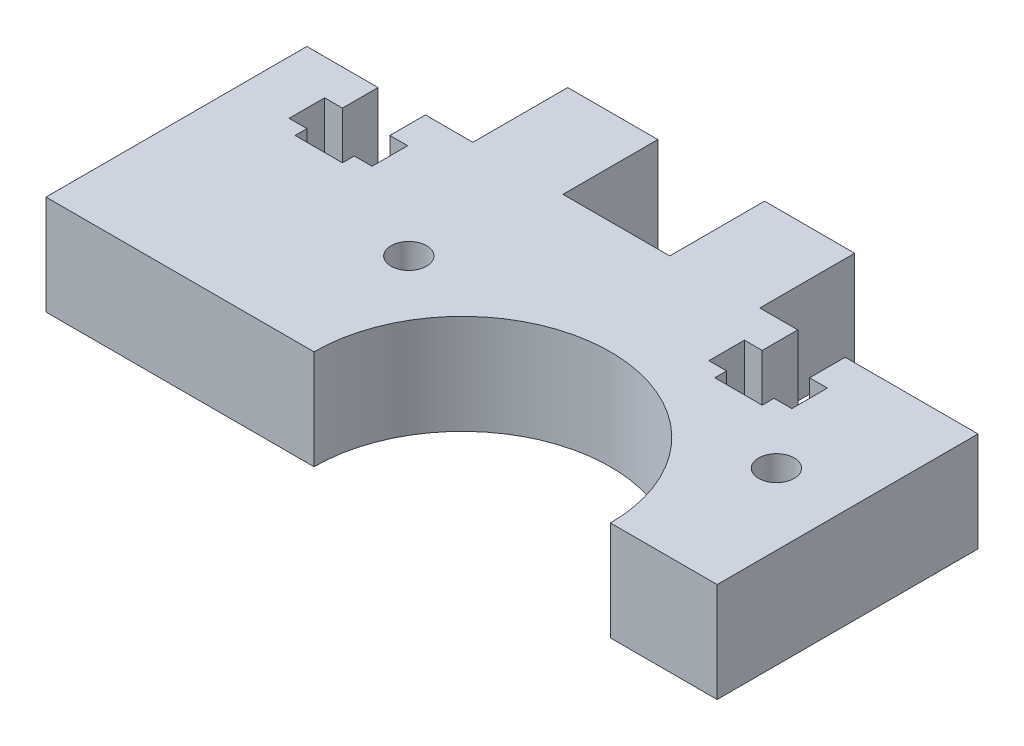
SolidWorks part; units mm, degrees
ref_plane "Front Plane" through (0, 0, 0) normal (0, 0, 1) x (1, 0, 0)
ref_plane "Top Plane" through (0, 0, 0) normal (0, 1, 0) x (1, 0, 0)
ref_plane "Right Plane" through (0, 0, 0) normal (1, 0, 0) x (0, 0, -1)
sketch "Sketch1" plane through (0, 0, 0) normal (0, 1, 0) x (1, 0, 0)
  line L0 (6.8, -11) -> (-8.7, 0) construction
  line L1 (-28.3, 11) -> (-22.3, 11)
  line L2 (-28.3, 11) -> (-28.3, -11)
  line L3 (-28.3, -11) -> (-5.7, -11)
  line L4 (28.3, 11) -> (28.3, -11)
  line L5 (-28.3, 11) -> (28.3, -11) construction
  line L6 (-28.3, -11) -> (28.3, 11) construction
  line L7 (6.8, -11) -> (6.8, 1.5) construction
  line L8 (19.3, -11) -> (19.3, 11) construction
  line L9 (19.3, -11) -> (28.3, -11)
  line L10 (-28.3, 19) -> (28.3, 19) construction
  line L11 (-14.3, 11) -> (-14.3, 19)
  line L12 (-14.3, 19) -> (-6.7, 19)
  line L13 (-6.7, 19) -> (-6.7, 11)
  line L14 (2.3, 11) -> (2.3, 19)
  line L15 (2.3, 19) -> (9.9, 19)
  line L16 (9.9, 19) -> (9.9, 11)
  line L17 (-6.7, 11) -> (2.3, 11)
  line L18 (9.9, 11) -> (13.1, 11)
  line L19 (-20.3, 11) -> (-20.3, 4) construction
  line L20 (-18.3, 4) -> (-22.3, 4)
  line L21 (-22.3, 4) -> (-22.3, 5)
  line L22 (-22.3, 5) -> (-23.8, 5)
  line L23 (-23.8, 5) -> (-23.8, 8)
  line L24 (-23.8, 8) -> (-22.3, 8)
  line L25 (-22.3, 8) -> (-22.3, 11)
  line L26 (-22.3, 8) -> (-22.3, 5) construction
  line L27 (-18.3, 8) -> (-18.3, 5) construction
  line L28 (-18.3, 8) -> (-18.3, 11)
  line L29 (-16.8, 8) -> (-18.3, 8)
  line L30 (-16.8, 5) -> (-16.8, 8)
  line L31 (-18.3, 5) -> (-16.8, 5)
  line L32 (-18.3, 4) -> (-18.3, 5)
  line L33 (-18.3, 11) -> (-14.3, 11)
  line L34 (-2.6, 11) -> (-2.6, -11) construction
  line L35 (13.1, 8) -> (13.1, 5) construction
  line L36 (17.1, 8) -> (17.1, 5) construction
  line L37 (15.1, 11) -> (15.1, 4) construction
  line L38 (13.1, 4) -> (13.1, 5)
  line L39 (13.1, 5) -> (11.6, 5)
  line L40 (11.6, 5) -> (11.6, 8)
  line L41 (11.6, 8) -> (13.1, 8)
  line L42 (13.1, 8) -> (13.1, 11)
  line L43 (17.1, 8) -> (17.1, 11)
  line L44 (18.6, 8) -> (17.1, 8)
  line L45 (18.6, 5) -> (18.6, 8)
  line L46 (17.1, 5) -> (18.6, 5)
  line L47 (17.1, 4) -> (17.1, 5)
  line L48 (13.1, 4) -> (17.1, 4)
  line L49 (17.1, 11) -> (28.3, 11)
  line L50 (-10.5, 19) -> (-10.5, 11) construction
  line L51 (6.1, 19) -> (6.1, 11) construction
  arc A0 (19.3, -11) -> (-5.7, -11) centre (6.8, -11) ccw
  circle A1 centre (-8.7, 0) radius 1.5
  circle A2 centre (22.3, 0) radius 1.5
  point P0 (0, 0)
  dimension "D3" = 25
  dimension "D4" = 3
  dimension "D1" = 56.6
  dimension "D2" = 22
  dimension "D5" = 15.5
  dimension "D6" = 11
  dimension "D7" = 9
  dimension "D8" = 8
  dimension "D9" = 7.6
  dimension "D10" = 7.6
  dimension "D11" = 9
  dimension "D12" = 14
  dimension "D13" = 7
  dimension "D14" = 2
  dimension "D15" = 1.5
  dimension "D16" = 3
  dimension "D17" = 6
  dimension "D18" = 1
  dimension "D19" = 2
  dimension "D20" = 3
  dimension "D21" = 3.2
extrude "Boss-Extrude1" add sketch "Sketch1" along normal blind 8.4
